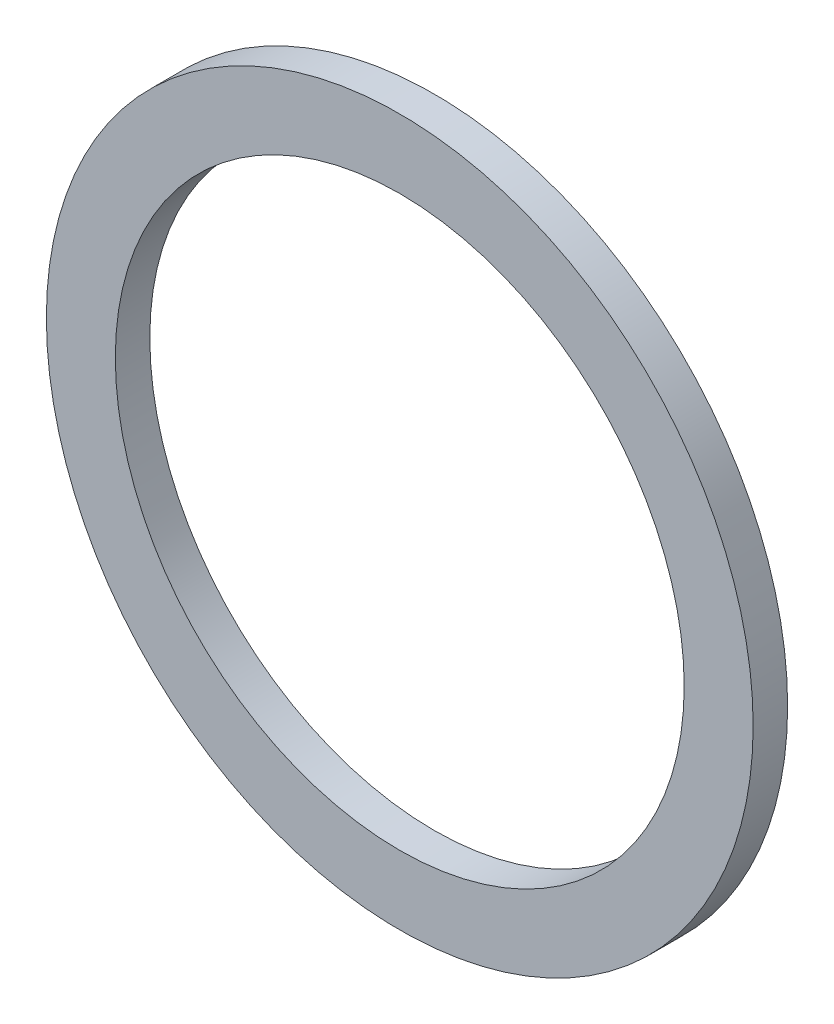
SolidWorks part; units mm, degrees
ref_plane "Plan de face" through (0, 0, 0) normal (0, 0, 1) x (1, 0, 0)
ref_plane "Plan de dessus" through (0, 0, 0) normal (0, 1, 0) x (1, 0, 0)
ref_plane "Plan de droite" through (0, 0, 0) normal (1, 0, 0) x (0, 0, -1)
sketch "Esquisse1" plane through (0, 0, 0) normal (0, 0, 1) x (1, 0, 0)
  circle A0 centre (0, 0) radius 8.25
  circle A1 centre (0, 0) radius 10.25
  dimension "D1" = 16.5
  dimension "D2" = 20.5
extrude "Extrusion1" add sketch "Esquisse1" along normal mid plane 1
